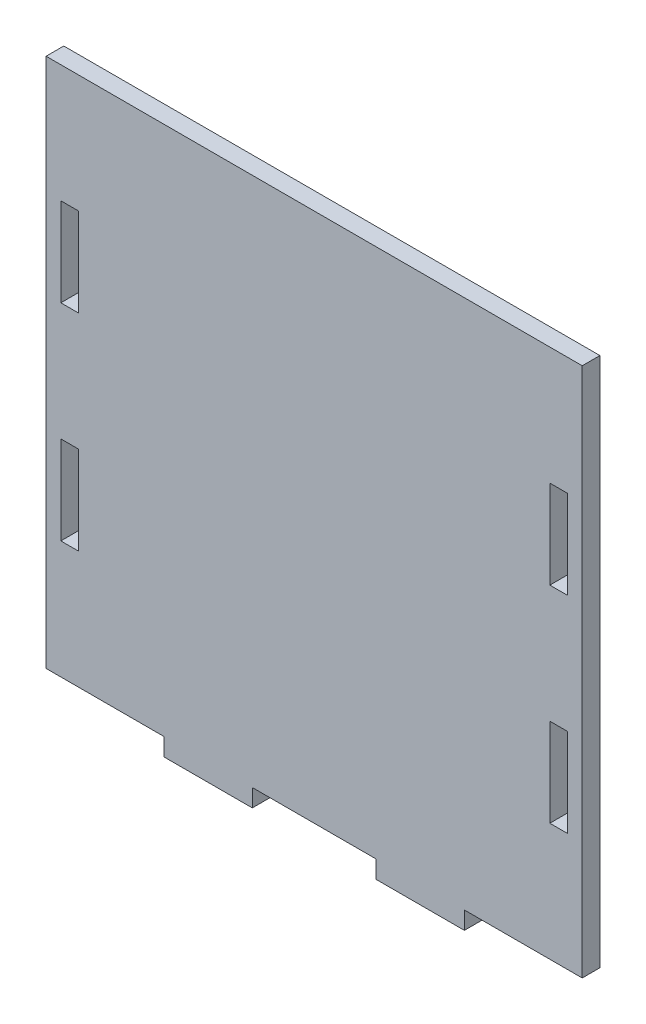
SolidWorks part; units mm, degrees
ref_plane "Front Plane" through (0, 0, 0) normal (0, 0, 1) x (1, 0, 0)
ref_plane "Top Plane" through (0, 0, 0) normal (0, 1, 0) x (1, 0, 0)
ref_plane "Right Plane" through (0, 0, 0) normal (1, 0, 0) x (0, 0, -1)
sketch "Sketch1" plane through (0, 0, 0) normal (0, 0, 1) x (1, 0, 0)
  line L0 (0, 0) -> (-45.5, 0) construction
  line L1 (-45.5, 45) -> (45.5, 45)
  line L2 (-45.5, 45) -> (-45.5, -45)
  line L3 (-45.5, -45) -> (45.5, -45)
  line L4 (45.5, 45) -> (45.5, -45)
  line L5 (-45.5, 45) -> (45.5, -45) construction
  line L6 (-45.5, -45) -> (45.5, 45) construction
  line L7 (-25.5, -45) -> (-10.5, -45)
  line L8 (-25.5, -45) -> (-25.5, -48)
  line L9 (-25.5, -48) -> (-10.5, -48)
  line L10 (-10.5, -45) -> (-10.5, -48)
  line L11 (10.5, -45) -> (25.5, -45)
  line L12 (10.5, -45) -> (10.5, -48)
  line L13 (10.5, -48) -> (25.5, -48)
  line L14 (25.5, -45) -> (25.5, -48)
  line L15 (0, 0) -> (0, -45) construction
  line L16 (10.5, 48) -> (25.5, 48)
  line L17 (25.5, 45) -> (25.5, 48)
  line L18 (10.5, 45) -> (25.5, 45)
  line L19 (10.5, 45) -> (10.5, 48)
  line L20 (-25.5, 48) -> (-10.5, 48)
  line L21 (-10.5, 45) -> (-10.5, 48)
  line L22 (-25.5, 45) -> (-10.5, 45)
  line L23 (-25.5, 45) -> (-25.5, 48)
  line L24 (-43, -25) -> (-40, -25)
  line L25 (43, 25) -> (40, 25)
  line L26 (43, 25) -> (43, 10)
  line L27 (43, 10) -> (40, 10)
  line L28 (40, 25) -> (40, 10)
  line L29 (43, -10) -> (40, -10)
  line L30 (43, -10) -> (43, -25)
  line L31 (43, -25) -> (40, -25)
  line L32 (40, -10) -> (40, -25)
  line L33 (-40, -10) -> (-40, -25)
  line L34 (-43, -10) -> (-40, -10)
  line L35 (-43, -10) -> (-43, -25)
  line L36 (-43, 10) -> (-40, 10)
  line L37 (-40, 25) -> (-40, 10)
  line L38 (-43, 25) -> (-40, 25)
  line L39 (-43, 25) -> (-43, 10)
  point P0 (0, 0)
  dimension "D1" = 91
  dimension "D2" = 90
  dimension "D3" = 3
  dimension "D4" = 3
  dimension "D5" = 15
  dimension "D6" = 15
  dimension "D7" = 20
  dimension "D8" = 20
  dimension "D9" = 3
  dimension "D10" = 15
  dimension "D11" = 20
  dimension "D12" = 20
  dimension "D13" = 15
  dimension "D14" = 3
  dimension "D15" = 2.5
  dimension "D16" = 2.5
extrude "Boss-Extrude1" add sketch "Sketch1" along normal blind 3 contours L4 L1 L2 L3 L39 L38 L37 L36 L35 L34 L33 L24 L32 L29 L30 L31 L28 L25 L26 L27 | L10 L3 L8 L9 | L14 L3 L12 L13
